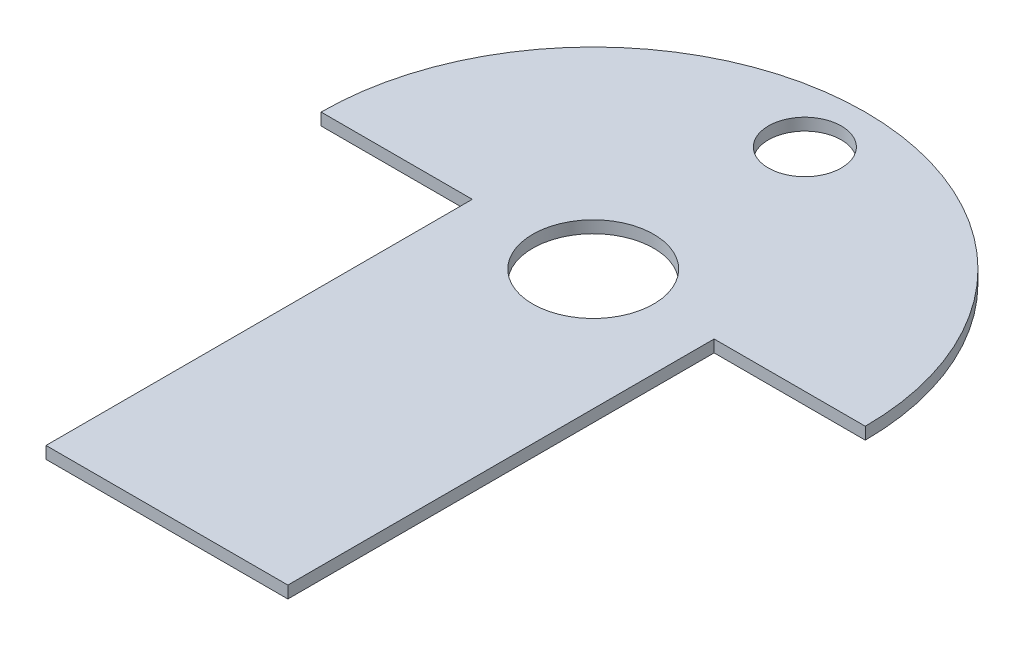
SolidWorks part; units mm, degrees
ref_plane "Plan de face" through (0, 0, 0) normal (0, 0, 1) x (1, 0, 0)
ref_plane "Plan de dessus" through (0, 0, 0) normal (0, 1, 0) x (1, 0, 0)
ref_plane "Plan de droite" through (0, 0, 0) normal (1, 0, 0) x (0, 0, -1)
sketch "Esquisse1" plane through (0, 0, 0) normal (0, 1, 0) x (1, 0, 0)
  line L0 (-50, 40.5) -> (40, 40.5)
  line L1 (-25, 40.5) -> (15, 40.5)
  line L2 (-25, 40.5) -> (-25, -30)
  line L3 (-25, -30) -> (15, -30)
  line L4 (15, 40.5) -> (15, -30)
  arc A0 (40, 40.5) -> (-50, 40.5) centre (-5, 40.5) ccw
  dimension "D5" = 90
  dimension "D1" = 40
  dimension "D2" = 70.5
  dimension "D3" = 25
  dimension "D4" = 30
extrude "Boss.-Extru.1" add sketch "Esquisse1" along normal blind 2 contours L4 L0 L2 L3 | L0 A0
sketch "Esquisse2" plane through (0, 2, 0) normal (0, 1, 0) x (1, 0, 0)
  line L0 (-50, 40.5) -> (-25, 40.5) construction
  line L1 (15, 40.5) -> (15, -30) construction
  circle A0 centre (-5, 40.5) radius 10
  dimension "D1" = 20
  dimension "D2" = 0
  dimension "D3" = 20
extrude "Enlèv. mat.-Extru.1" cut sketch "Esquisse2" against normal blind 2
sketch "Esquisse3" plane through (0, 0, 0) normal (0, -1, 0) x (-1, 0, 0)
  line L1 (-15, 40.5) -> (-40, 40.5) construction
  line L2 (-15, 40.5) -> (-15, -30) construction
  circle A0 centre (5, 75.5) radius 6.03
  dimension "D1" = 12.06
  dimension "D2" = 35
  dimension "D3" = 20
extrude "Enlèv. mat.-Extru.2" cut sketch "Esquisse3" against normal blind 10
